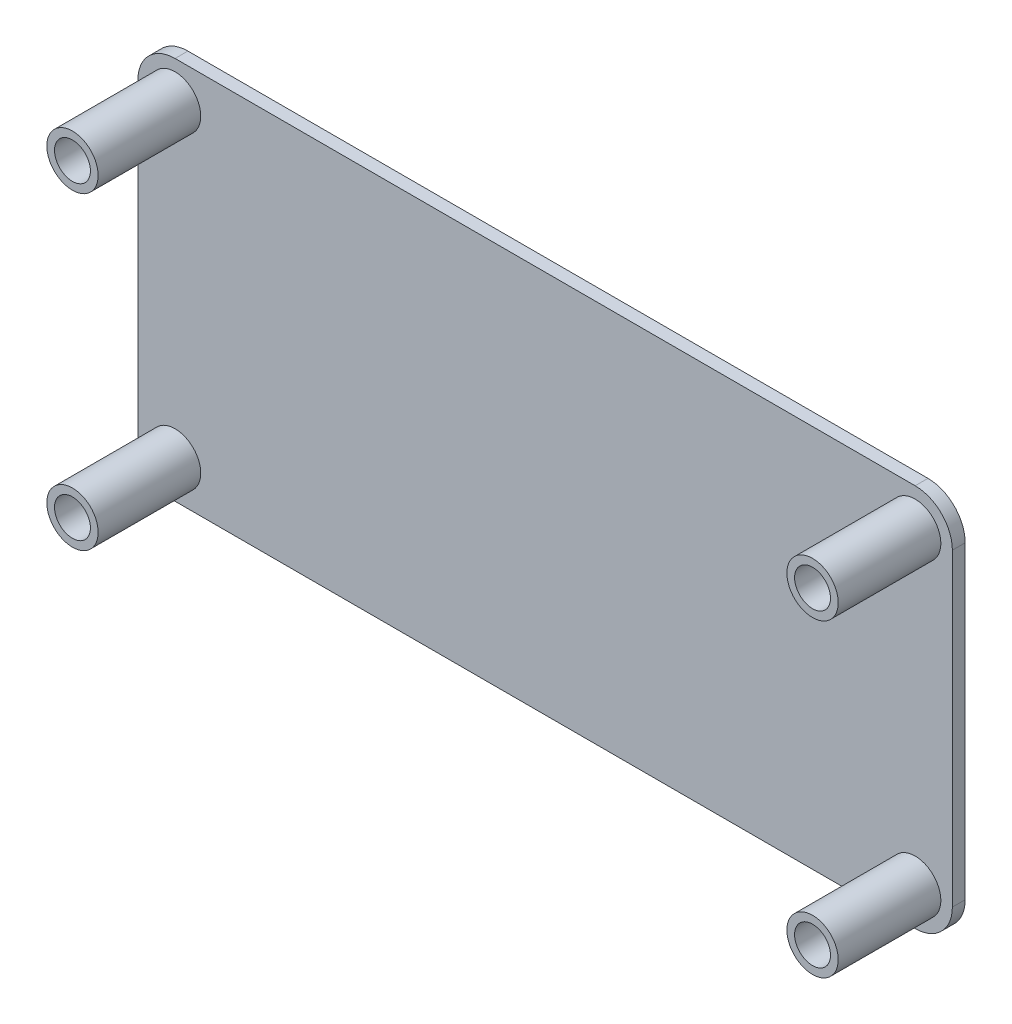
SolidWorks part; units mm, degrees
ref_plane "前视基准面" through (0, 0, 0) normal (0, 0, 1) x (1, 0, 0)
ref_plane "上视基准面" through (0, 0, 0) normal (0, 1, 0) x (1, 0, 0)
ref_plane "右视基准面" through (0, 0, 0) normal (1, 0, 0) x (0, 0, -1)
sketch "草图1" plane through (0, 0, 0) normal (0, 0, 1) x (1, 0, 0)
  line L13 (0, -2.9) -> (57.7, -2.9)
  line L21 (0, 27) -> (57.7, 27)
  line L22 (-2.9, 0) -> (-2.9, 24.1)
  line L23 (60.6, 0) -> (60.6, 24.1)
  arc A25 (0, -2.9) -> (-2.9, 0) centre (0, 0) cw
  arc A26 (0, 27) -> (-2.9, 24.1) centre (0, 24.1) ccw
  arc A27 (60.6, 24.1) -> (57.7, 27) centre (57.7, 24.1) ccw
  arc A28 (57.7, -2.9) -> (60.6, 0) centre (57.7, 0) ccw
extrude "凸台-拉伸1" add sketch "草图1" along normal blind 1
sketch "草图3" plane through (0, 0, 0) normal (0, 0, 1) x (1, 0, 0)
  circle A29 centre (0, 24.1) radius 1.4
  circle A30 centre (0, 0) radius 2
  circle A31 centre (0, 0) radius 1.4
  circle A32 centre (57.7, 0) radius 1.4
  circle A33 centre (57.7, 24.1) radius 1.4
  circle A34 centre (0, 24.1) radius 2
  circle A35 centre (57.7, 0) radius 2
  circle A36 centre (57.7, 24.1) radius 2
extrude "凸台-拉伸3" add sketch "草图3" along normal blind 9
